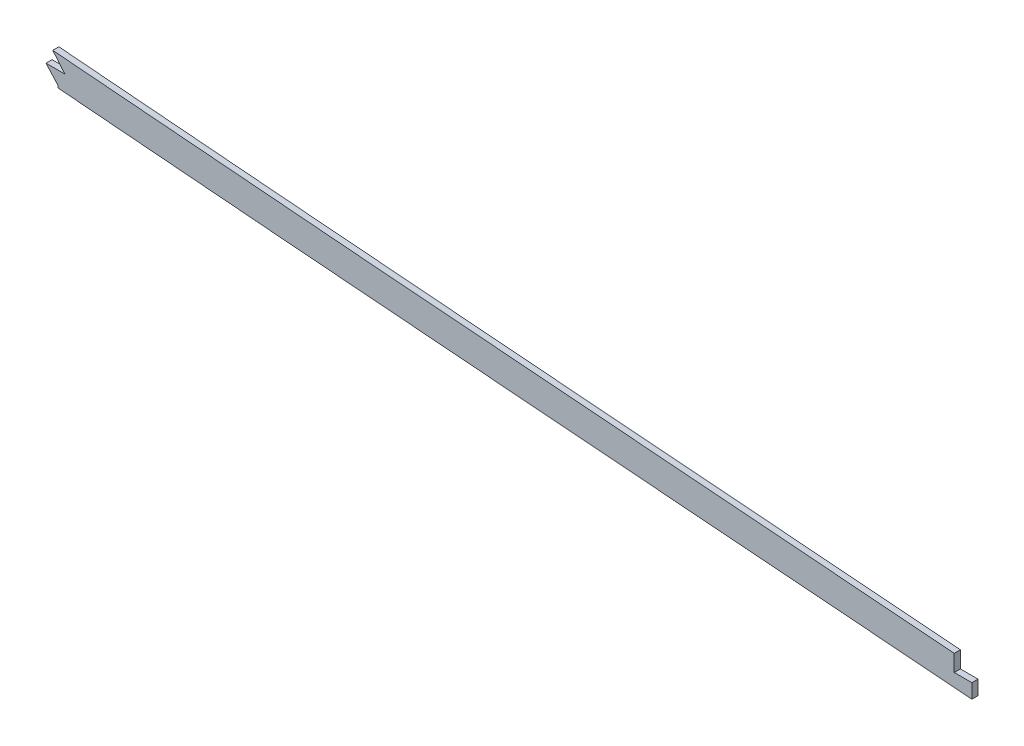
SolidWorks part; units mm, degrees
ref_plane "Front Plane" through (0, 0, 0) normal (0, 0, 1) x (1, 0, 0)
ref_plane "Top Plane" through (0, 0, 0) normal (0, 1, 0) x (1, 0, 0)
ref_plane "Right Plane" through (0, 0, 0) normal (1, 0, 0) x (0, 0, -1)
sketch "Sketch2" plane through (0, 0, 0) normal (0, 0, 1) x (1, 0, 0)
  line L0 (0, 0) -> (266.9553, 0) construction
  line L1 (825.5, 263.7287) -> (825.5, 174.6622)
  line L2 (2491.74, 117.5472) -> (2491.74, 52.664)
  spline S0 degree 5 poles (818.067, 264.7065) (827.0431, 263.4992) (836.0291, 262.3734) (845.0868, 261.3058) (891.3865, 256.087) (937.6862, 251.7792) (973.4521, 248.2277) (1071.9467, 239.0511) (1170.4413, 229.7315) (1231.7919, 224.5039) (1324.8993, 216.7906) (1418.0067, 209.0401) (1449.7429, 206.3618) (1636.9286, 190.5211) (1824.1143, 175.4092) (1979.9669, 164.2997) (2156.2686, 150.4144) (2332.5703, 133.8572) (2354.213, 131.7851) (2436.3555, 123.724) (2518.4981, 114.8591) (2579.4813, 107.7425) (2639.6368, 100.3834) (2699.7923, 92.6045) knots 77.930822 77.930822 77.930822 77.930822 77.930822 77.930822 82.465793 82.465793 82.465793 100.79329 100.79329 100.79329 131.098954 131.098954 131.098954 146.769198 146.769198 146.769198 223.533959 223.533959 223.533959 233.943117 233.943117 233.943117 264.216209 264.216209 264.216209 264.216209 264.216209 264.216209 weights 1 1 1 1 1 1 1 1 1 1 1 1 1 1 1 1 1 1 1 1 1 1 1 1
  spline S1 degree 1 poles (816.0355, 249.6025) (2697.8379, 77.4903) knots 0 0 1 1 construction
  spline S2 degree 3 poles (816.0355, 249.6025) (820.896, 248.9488) (830.6112, 247.6997) (845.2811, 245.9534) (860.0865, 244.2956) (879.8307, 242.1866) (904.37, 239.6983) (933.571, 236.8322) (962.6427, 234.0237) (991.7626, 231.242) (1021.072, 228.4759) (1060.3764, 224.797) (1109.513, 220.1844) (1168.5112, 214.8171) (1227.5001, 209.6621) (1306.1332, 203.0212) (1404.3615, 194.9207) (1522.2399, 184.9181) (1640.1829, 175.167) (1758.1654, 165.7576) (1876.1554, 156.5909) (1994.0875, 147.4533) (2092.2687, 139.6242) (2170.748, 133.0797) (2219.7717, 128.8422) (2258.984, 125.3472) (2288.3795, 122.6709) (2317.8122, 119.9317) (2347.5515, 117.1004) (2377.1599, 114.2101) (2406.4697, 111.269) (2435.8183, 108.2401) (2474.9139, 104.0902) (2523.7162, 98.6933) (2582.0419, 91.9123) (2640.0752, 84.8576) (2678.5742, 79.9814) (2697.8379, 77.4903) knots 77.930822 77.930822 77.930822 77.930822 79.386176 80.841531 82.296885 83.75224 86.662949 89.573658 92.484367 95.395077 98.305786 101.216495 107.037913 112.859332 118.68075 124.502168 136.145005 147.787842 159.430678 171.073515 182.716352 194.359189 206.002025 211.823444 217.644862 220.555571 223.46628 226.37699 229.287699 232.198408 235.109117 238.019826 240.930535 246.751954 252.573372 258.39479 264.216209 264.216209 264.216209 264.216209
  spline S3 degree 5 poles (818.067, -264.7065) (827.0431, -263.4992) (836.0291, -262.3734) (845.0868, -261.3058) (891.3865, -256.087) (937.6862, -251.7792) (973.4521, -248.2277) (1071.9467, -239.0511) (1170.4413, -229.7315) (1231.7919, -224.5039) (1324.8993, -216.7906) (1418.0067, -209.0401) (1449.7429, -206.3618) (1636.9286, -190.5211) (1824.1143, -175.4092) (1979.9669, -164.2997) (2156.2686, -150.4144) (2332.5703, -133.8572) (2354.213, -131.7851) (2436.3555, -123.724) (2518.4981, -114.8591) (2579.4813, -107.7425) (2639.6368, -100.3834) (2699.7923, -92.6045) knots 77.930822 77.930822 77.930822 77.930822 77.930822 77.930822 82.465793 82.465793 82.465793 100.79329 100.79329 100.79329 131.098954 131.098954 131.098954 146.769198 146.769198 146.769198 223.533959 223.533959 223.533959 233.943117 233.943117 233.943117 264.216209 264.216209 264.216209 264.216209 264.216209 264.216209 weights 1 1 1 1 1 1 1 1 1 1 1 1 1 1 1 1 1 1 1 1 1 1 1 1
  point P2 (0, 0)
  dimension "D1" = 818.067
  dimension "D2" = 825.5
  dimension "D3" = 2491.74
  dimension "D4" = 15.24
extrude "Boss-Extrude1" add sketch "Sketch2" along normal mid plane 3.175 contours L1 S2 L2 S0
fillet "Fillet1" radius 2.54 4 edges at (2491.74, 102.2148, 0) (825.5, 248.3644, 0)
sketch "Sketch3" plane through (0, 0, 1.5875) normal (0, 0, 1) x (1, 0, 0)
  line L0 (1554.7817, 197.537) -> (1554.7817, 212.262)
  line L4 (1554.7817, 197.537) -> (1561.1242, 190.0292)
  line L5 (1561.1242, 190.0292) -> (1551.3118, 190.0292)
  line L6 (1551.3118, 190.0292) -> (1557.6111, 183.0636)
  line L7 (2021.3026, 160.5495) -> (2021.3026, 151.9732)
  line L8 (2021.3026, 151.9732) -> (2030.429, 151.9732)
  line L9 (2030.429, 151.9732) -> (2030.429, 144.5379)
  line L10 (1554.7817, 212.262) -> (810.4518, 281.004)
  line L11 (810.4518, 281.004) -> (810.4518, 218.4497)
  line L12 (810.4518, 218.4497) -> (1556.6438, 177.7371)
  line L13 (1556.6438, 177.7371) -> (1557.6111, 183.0636)
  line L14 (2021.3026, 160.5495) -> (2021.3026, 169.9717)
  line L15 (2021.3026, 169.9717) -> (2503.9897, 125.3935)
  line L16 (2503.9897, 125.3935) -> (2503.9897, 84.6282)
  line L17 (2503.9897, 84.6282) -> (2030.429, 141.7019)
  line L18 (2030.429, 141.7019) -> (2030.429, 144.5379)
  spline S0 degree 5 poles (828.3591, 263.3639) (835.3006, 262.485) (842.2713, 261.6451) (849.2939, 260.8336) (893.49, 255.8914) (937.6862, 251.7793) (973.4521, 248.2278) (1071.9467, 239.0512) (1170.4413, 229.7316) (1231.792, 224.504) (1324.8993, 216.7907) (1418.0067, 209.0402) (1449.7429, 206.3619) (1636.9286, 190.5212) (1824.1143, 175.4092) (1979.967, 164.2997) (2156.2686, 150.4145) (2332.5703, 133.8572) (2354.213, 131.7851) (2393.888, 127.8915) (2433.5631, 123.8105) (2452.2167, 121.8477) (2470.8575, 119.8423) (2489.4775, 117.7961) knots 78.969534 78.969534 78.969534 78.969534 78.969534 78.969534 82.465793 82.465793 82.465793 100.79329 100.79329 100.79329 131.098954 131.098954 131.098954 146.769198 146.769198 146.769198 223.533959 223.533959 223.533959 233.943117 233.943117 233.943117 243.183575 243.183575 243.183575 243.183575 243.183575 243.183575 weights 1 1 1 1 1 1 1 1 1 1 1 1 1 1 1 1 1 1 1 1 1 1 1 1 construction
  spline S1 degree 3 poles (827.7231, 248.0832) (828.6907, 247.9616) (834.5293, 247.2333) (845.2811, 245.9534) (860.0865, 244.2956) (879.8307, 242.1866) (904.37, 239.6983) (933.571, 236.8322) (962.6427, 234.0237) (991.7626, 231.242) (1021.072, 228.4759) (1060.3764, 224.797) (1109.513, 220.1844) (1168.5112, 214.8171) (1227.5001, 209.6621) (1306.1332, 203.0212) (1404.3615, 194.9207) (1522.2399, 184.9181) (1640.1829, 175.167) (1758.1654, 165.7576) (1876.1554, 156.5909) (1994.0875, 147.4533) (2092.2687, 139.6242) (2170.748, 133.0797) (2219.7717, 128.8422) (2258.984, 125.3472) (2288.3795, 122.6709) (2317.8122, 119.9317) (2347.5515, 117.1004) (2377.1599, 114.2101) (2406.4697, 111.269) (2435.8183, 108.2401) (2463.3021, 105.3227) (2480.9973, 103.397) (2488.9223, 102.5252) knots 79.096923 79.096923 79.096923 79.096923 79.386176 80.841531 82.296885 83.75224 86.662949 89.573658 92.484367 95.395077 98.305786 101.216495 107.037913 112.859332 118.68075 124.502168 136.145005 147.787842 159.430678 171.073515 182.716352 194.359189 206.002025 211.823444 217.644862 220.555571 223.46628 226.37699 229.287699 232.198408 235.109117 238.019826 240.930535 243.293903 243.293903 243.293903 243.293903 construction
extrude "Cut-Extrude1" cut sketch "Sketch3" against normal blind 7.62 contours L10 L11 L12 L13 L6 L5 L4 L0 | L15 L16 L17 L18 L9 L8 L7 L14
